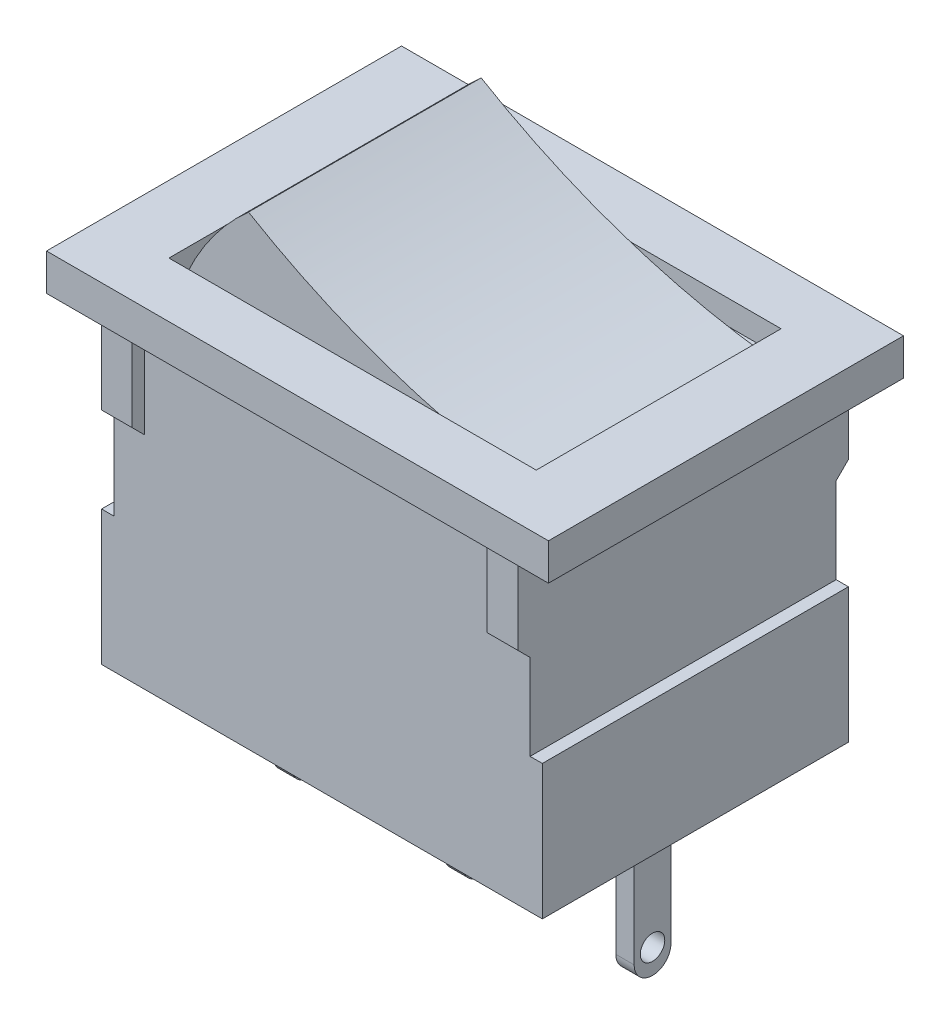
SolidWorks part; units mm, degrees
ref_plane "Спереди" through (0, 0, 0) normal (0, 0, 1) x (1, 0, 0)
ref_plane "Сверху" through (0, 0, 0) normal (0, 1, 0) x (1, 0, 0)
ref_plane "Справа" through (0, 0, 0) normal (1, 0, 0) x (0, 0, -1)
sketch "Эскиз1" plane through (0, 0, 0) normal (0, 0, 1) x (1, 0, 0)
  line L0 (0, 0) -> (0, 11)
  line L1 (0, 0) -> (18, 0)
  line L2 (0, 11) -> (18, 11)
  line L3 (18, 0) -> (18, 11)
  dimension "D1" = 18
  dimension "D2" = 11
extrude "Бобышка-Вытянуть1" add sketch "Эскиз1" along normal blind 12.5
sketch "Эскиз2" plane through (0, 11, 0) normal (0, 1, 0) x (1, 0, 0)
  line L0 (9, 0) -> (9, -12.5) construction
  line L1 (18, 0) -> (0, 0) construction
  line L2 (18, -12.5) -> (0, -12.5) construction
  line L3 (18, -6.25) -> (0, -6.25) construction
  line L4 (18, -12.5) -> (18, 0) construction
  line L5 (0, -12.5) -> (0, 0) construction
  line L7 (-1.25, 1) -> (19.25, 1)
  line L8 (-1.25, 1) -> (-1.25, -13.5)
  line L9 (-1.25, -13.5) -> (19.25, -13.5)
  line L10 (19.25, 1) -> (19.25, -13.5)
  line L11 (-1.25, 1) -> (19.25, -13.5) construction
  line L12 (-1.25, -13.5) -> (19.25, 1) construction
  point P12 (9, -6.25)
  dimension "D1" = 14.5
  dimension "D2" = 20.5
extrude "Бобышка-Вытянуть2" add sketch "Эскиз2" along normal blind 1.5
sketch "Эскиз3" plane through (0, 0, 12.5) normal (0, 0, 1) x (1, 0, 0)
  line L0 (18, 11) -> (17.5, 11)
  line L1 (18, 11) -> (18, 3.5)
  line L2 (17.5, 11) -> (17.5, 3.5)
  line L3 (18, 3.5) -> (17.5, 3.5)
  line L5 (9, 11) -> (9, 0) construction
  line L6 (18, 11) -> (0, 11) construction
  line L7 (0, 0) -> (18, 0) construction
  line L8 (0, 3.5) -> (0.5, 3.5)
  line L9 (0.5, 11) -> (0.5, 3.5)
  line L10 (0, 11) -> (0, 3.5)
  line L11 (0, 11) -> (0.5, 11)
  dimension "D1" = 0.5
  dimension "D2" = 7.5
extrude "Вырез-Вытянуть2" cut sketch "Эскиз3" against normal through all
sketch "Эскиз4" plane through (17.5, 0, 0) normal (1, 0, 0) x (0, 0, -1)
  line L0 (-12.5, 7) -> (-13, 7.5)
  line L1 (-12.5, 11) -> (-12.5, 3.5) construction
  line L2 (-13, 7.5) -> (-13, 11)
  line L3 (0, 11) -> (-12.5, 11) construction
  line L4 (-12.5, 11) -> (-13, 11)
  line L5 (-12.5, 11) -> (-12.5, 7)
  line L6 (-12.5, 0) -> (0, 0) construction
  line L7 (-14.7352, 0) -> (0, 0) construction
  dimension "D1" = 0.5
  dimension "D2" = 0.5
  dimension "D3" = 7
extrude "Бобышка-Вытянуть3" add sketch "Эскиз4" against normal blind 1.25
sketch "Эскиз5" plane through (18, 0, 0) normal (1, 0, 0) x (0, 0, -1)
  line L0 (-6.25, 0) -> (-6.25, 3.5) construction
  line L1 (-12.5, 0) -> (0, 0) construction
  line L2 (0, 3.5) -> (-12.5, 3.5) construction
ref_plane "Плоскость1" through (0, 0, 6.25) normal (0, 0, -1) x (0, 1, 0)
mirror "Зеркальное отражение1" about plane through (0, 0, 6.25) normal (0, 0, -1) of "Бобышка-Вытянуть3"
sketch "Эскиз6" plane through (0, 0, 0) normal (0, 0, -1) x (-1, 0, 0)
  line L0 (-9, 0) -> (-9, 11) construction
  line L1 (0, 0) -> (-18, 0) construction
  line L2 (-16.25, 11) -> (-0.5, 11) construction
ref_plane "Плоскость2" through (9, 0, 0) normal (-1, 0, 0) x (0, 1, 0)
mirror "Зеркальное отражение2" about plane through (9, 0, 0) normal (-1, 0, 0) of "Зеркальное отражение1", "Бобышка-Вытянуть3"
sketch "Эскиз7" plane through (0, 0, 0) normal (0, -1, 0) x (1, 0, 0)
  line L0 (0, 12.5) -> (18, 12.5) construction
  line L1 (18, 12.5) -> (18, 0) construction
  line L2 (0, 12.5) -> (0, 0) construction
  line L3 (0, 0) -> (18, 0) construction
  line L4 (0, 12.5) -> (18, 12.5)
  line L5 (18, 12.5) -> (18, 0)
  line L6 (0, 12.5) -> (0, 0)
  line L7 (0, 0) -> (18, 0)
extrude "Бобышка-Вытянуть4" add sketch "Эскиз7" along normal blind 2
sketch "Эскиз8" plane through (0, 12.5, 0) normal (0, 1, 0) x (1, 0, 0)
  line L0 (-1.25, -6.25) -> (19.25, -6.25) construction
  line L1 (-1.25, 1) -> (-1.25, -13.5) construction
  line L2 (19.25, -13.5) -> (19.25, 1) construction
  line L3 (9, 1) -> (9, -13.5) construction
  line L4 (19.25, 1) -> (-1.25, 1) construction
  line L5 (-1.25, -13.5) -> (19.25, -13.5) construction
  line L7 (1.5, -1.25) -> (16.5, -1.25)
  line L8 (1.5, -1.25) -> (1.5, -11.25)
  line L9 (1.5, -11.25) -> (16.5, -11.25)
  line L10 (16.5, -1.25) -> (16.5, -11.25)
  line L11 (1.5, -1.25) -> (16.5, -11.25) construction
  line L12 (1.5, -11.25) -> (16.5, -1.25) construction
  point P12 (9, -6.25)
  dimension "D1" = 15
  dimension "D2" = 10
extrude "Вырез-Вытянуть3" cut sketch "Эскиз8" against normal blind 1
sketch "Эскиз9" plane through (0, 0, 6.25) normal (0, 0, -1) x (0, 1, 0)
  line L0 (11.5, 1.5) -> (11.5, 16.5) construction
  line L1 (11.5, 4.5) -> (15.5, 4.5) construction
  line L3 (11.5, 1.5) -> (12.5, 1.5) construction
  line L4 (11.5, 1.5) -> (12.5, 1.5) construction
  line L5 (11.5, 1.75) -> (11.5, 16.25)
  arc A0 (11.5, 1.75) -> (15.5, 4.5) centre (8.0041, 11.119) ccw
  arc A1 (15.5, 4.5) -> (11.5, 16.25) centre (41.2852, 19.8338) cw
  point P6 (11.5, 1.75)
  point P8 (11.5, 16.25)
  dimension "D5" = 20
  dimension "D6" = 30
  dimension "D1" = 4
  dimension "D2" = 3
  dimension "D3" = 0.25
  dimension "D4" = 0.25
extrude "Бобышка-Вытянуть5" add sketch "Эскиз9" along normal blind 4.75 and the other way blind 4.75
sketch "Эскиз10" plane through (0, -2, 0) normal (0, -1, 0) x (1, 0, 0)
  line L0 (0, 6.25) -> (18, 6.25) construction
  line L1 (0, 12.5) -> (0, 0) construction
  line L2 (18, 0) -> (18, 12.5) construction
  line L3 (1.5, 0) -> (1.5, 12.5) construction
  line L4 (0, 0) -> (18, 0) construction
  line L5 (18, 12.5) -> (0, 12.5) construction
  dimension "D1" = 1.5
ref_plane "Плоскость3" through (1.5, 0, 0) normal (1, 0, 0) x (0, 0, 1)
sketch "Эскиз11" plane through (1.5, 0, 0) normal (1, 0, 0) x (0, 0, 1)
  line L0 (5.5, 2) -> (5.5, 7.25)
  line L1 (0, 2) -> (12.5, 2) construction
  line L2 (6.25, 2) -> (6.25, 8) construction
  line L3 (7, 2) -> (7, 7.25)
  line L4 (5.5, 2) -> (7, 2)
  arc A0 (5.5, 7.25) -> (6.25, 8) centre (6.25, 7.25) cw
  arc A1 (6.25, 8) -> (7, 7.25) centre (6.25, 7.25) cw
  circle A2 centre (6.25, 7) radius 0.5
  dimension "D2" = 6
  dimension "D3" = 0.75
  dimension "D4" = 1
  dimension "D5" = 5
  dimension "D1" = 1.5
extrude "Бобышка-Вытянуть6" add sketch "Эскиз11" along normal blind 0.75
pattern_linear "Линейный массив1" count 3 spacing 7 along (1, 0, 0) of "Бобышка-Вытянуть6"
sketch "Эскиз12" plane through (0, 12.5, 0) normal (0, 1, 0) x (1, 0, 0)
  line L0 (19.25, -6.25) -> (-1.6156, -6.25) construction
  line L1 (19.25, -13.5) -> (19.25, 1) construction
  line L2 (9, 1) -> (9, -13.5) construction
  line L3 (19.25, 1) -> (-1.25, 1) construction
  line L4 (-1.25, -13.5) -> (19.25, -13.5) construction
